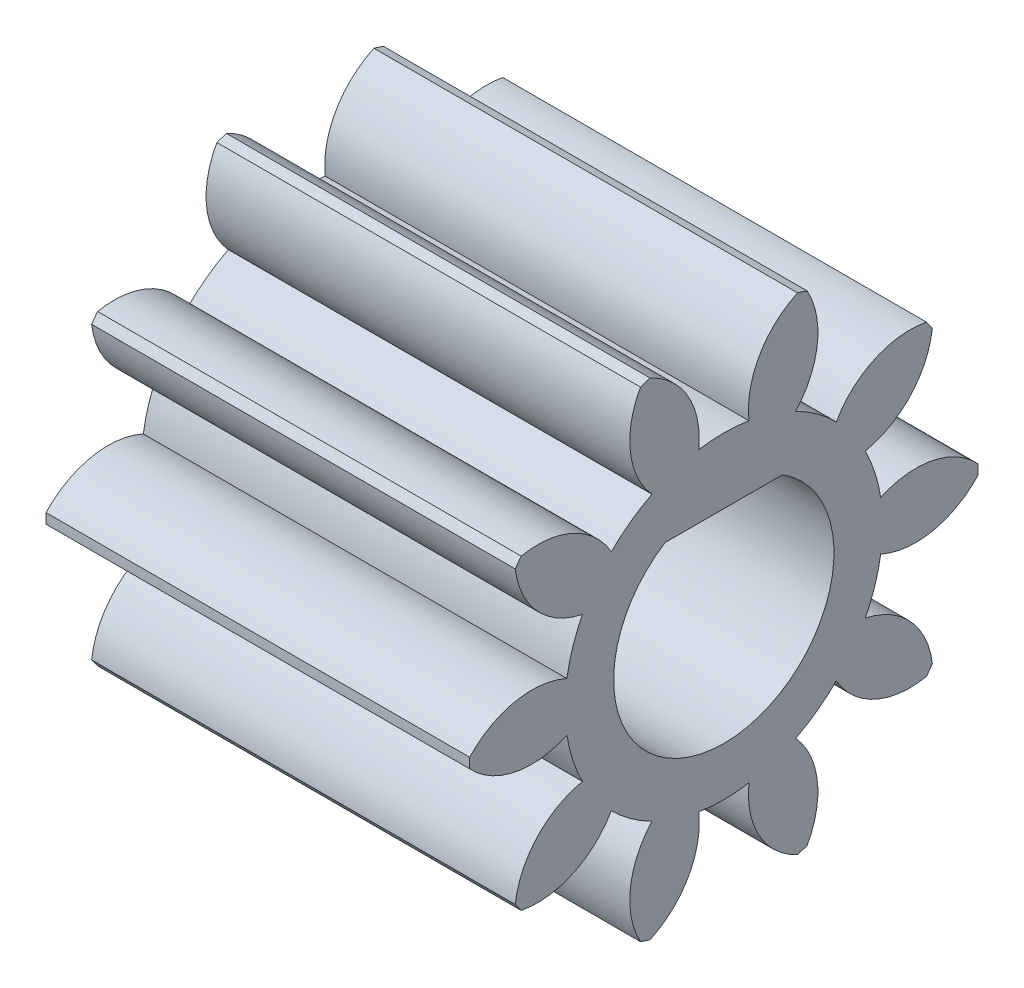
SolidWorks part; units mm, degrees
ref_plane "Plane1" through (0, 0, 0) normal (0, 0, 1) x (1, 0, 0)
ref_plane "Plane2" through (0, 0, 0) normal (0, 1, 0) x (1, 0, 0)
ref_plane "Plane3" through (0, 0, 0) normal (1, 0, 0) x (0, 0, -1)
other "Configuration Table"
sketch "HoldingSke" plane through (0, 0, 0) normal (0, 1, 0) x (1, 0, 0)
  line L0 (0, 0) -> (0.9848, -0.1736)
  line L1 (-15, 0) -> (100, 0) construction
  line L2 (0, 0) -> (-2.1039, 2.3779)
  line L3 (0, 0) -> (-11.863, 4.5341)
  line L4 (0, 0) -> (8.5048, 1.4996)
  line L5 (0, 0) -> (-46.8476, -17.4728)
  line L6 (0, 0) -> (-8.2896, -5.593)
  line L7 (-2.1039, 2.3779) -> (8.6586, 51.2059)
  line L8 (-76.2, 54.61) -> (-75.3, 54.61)
  line L9 (-71.009, 38.7566) -> (-53.1078, 45.2721)
  line L10 (-76.2, 71.12) -> (104.1128, 71.12)
  line L11 (0, 0) -> (-10, 0)
  line L12 (-76.2, 101.6) -> (-76.162, 101.6)
  line L13 (24.9733, 27.94) -> (52.9518, 28.4284)
  line L14 (24.9733, 27.94) -> (24.9743, 27.94)
  line L15 (24.9733, 27.94) -> (100.4006, 29.5858)
  line L16 (-63.627, -1) -> (-12.827, -1)
  circle A0 centre (0, 0) radius 2.5
  circle A1 centre (0, 0) radius 3.749
  circle A2 centre (0, 0) radius 37.5
  circle A3 centre (0, 0) radius 2.5
  dimension "MHD" = 7.498
  dimension "Hub_dia" = 75
  dimension "Bore" = 5
  dimension "MBD" = 5
  dimension "Num_teeth" = 10
  dimension "Pitch" = 1
  dimension "Overall_len" = 50
  dimension "Show_teeth" = 10
  dimension "Thickness" = 10
  dimension "OAL" = 50.0001
  dimension "T_dim" = 0.9
  dimension "Ap" = 20
  dimension "H" = 19.05
  dimension "Pitch_radius" = 180.3128
  dimension "Width" = 10
  dimension "Backlash" = 0.038
  dimension "Addendum_fac" = 1
  dimension "Dedendum_fac" = 1.25
  dimension "Clearance_fac" = 0.25
  dimension "Dedendum_add" = 0.001
  dimension "Module" = 1
sketch "BasProSke" plane through (0, 0, 0) normal (0, 1, 0) x (1, 0, 0)
  line L0 (-10, 0) -> (60, 0) construction
  line L1 (0, 0) -> (0, 6)
  line L2 (0, 0) -> (10, 0)
  line L3 (10, 0) -> (10, 6)
  line L4 (10, 6) -> (0, 6)
  dimension "Thickness" = 10
  dimension "Diameter" = 12
revolve "Base-Revolve" add sketch "BasProSke" angle 360 about L0
sketch "TooCutSke" plane through (0, 0, 0) normal (1, 0, 0) x (0, 0, -1)
  line L1 (0, 0) -> (0, 107) construction
  line L2 (0, 0) -> (-0.8485, 4.9275) construction
  line L3 (0, 0) -> (-3.0584, 9.4126) construction
  line L4 (-0.8485, 4.9275) -> (-1.5292, 4.7063) construction
  arc A0 (0.5928, 3.7018) -> (-0.5928, 3.7018) centre (0, 0) ccw
  arc A1 (1.7758, 5.7578) -> (-1.7758, 5.7578) centre (0, 0) ccw
  circle A2 centre (0, 0) radius 5 construction
  circle A3 centre (0, 0) radius 4.6985 construction
  arc A4 (-0.5928, 3.7018) -> (-1.7758, 5.7578) centre (-2.5801, 3.9267) ccw
  arc A5 (1.7758, 5.7578) -> (0.5928, 3.7018) centre (2.5801, 3.9267) ccw
  dimension "Root_dia" = 7.498
  dimension "Overcut_dia" = 12.0508
  dimension "Pitch_dia" = 10
  dimension "Base_dia" = 9.3969
  dimension "Flank_rad" = 2
  dimension "Half_ang" = 18
  dimension "Half_CT" = 0.7157
extrude "ToothCut" cut sketch "TooCutSke" along normal through all
fillet "Breaks" [suppressed] radius 0.02
fillet "RootFillets" [suppressed] radius 0.251
pattern_circular "TeethCuts" count 10 every 36 about axis through (-10, 0, 0) along (1, 0, 0) of "ToothCut", "RootFillets", "Breaks"
sketch "HubNeaOneSke" plane through (0, 0, 0) normal (-1, 0, 0) x (0, 0, 1)
  circle A0 centre (0, 0) radius 3.749
  dimension "Diameter" = 7.498
extrude "HubNearOne" [suppressed] add sketch "HubNeaOneSke" along normal blind 40.0001
sketch "HubNeaBotSke" plane through (0, 0, 0) normal (-1, 0, 0) x (0, 0, 1)
  circle A0 centre (0, 0) radius 3.749
  dimension "Diameter" = 7.498
extrude "HubNearBoth" [suppressed] add sketch "HubNeaBotSke" along normal blind 20
ref_plane "FarPln" through (10, 0, 0) normal (1, 0, 0) x (0, 0, -1)
sketch "HubFarSke" plane through (10, 0, 0) normal (1, 0, 0) x (0, 0, -1)
  circle A0 centre (0, 0) radius 3.749
  dimension "Diameter" = 7.498
extrude "HubFar" [suppressed] add sketch "HubFarSke" along normal blind 20
sketch "BorSke" plane through (0, 0, 0) normal (1, 0, 0) x (0, 0, -1)
  circle A0 centre (0, 0) radius 2.5
  dimension "Diameter" = 5
extrude "Bore" cut sketch "BorSke" along normal mid plane 100.0001
sketch "KeySke" plane through (0, 0, 0) normal (1, 0, 0) x (0, 0, -1)
  line L0 (-1, 0) -> (-1, 3.4)
  line L1 (-1, 3.4) -> (1, 3.4)
  line L2 (1, 3.4) -> (1, 0)
  line L3 (0, 0) -> (0, 34) construction
  line L4 (-1, 0) -> (1, 0)
  dimension "Offset" = 3.4
  dimension "Width" = 2
extrude "Keyway" [suppressed] cut sketch "KeySke" along normal mid plane 100.0001
pattern_circular "Keyway2" [suppressed] count 2 every 90 about axis through (-10, 0, 0) along (1, 0, 0)
sketch "Sketch1" plane through (10, 0, 0) normal (1, 0, 0) x (0, 0, -1)
  line L0 (0, 0) -> (2.4, 0) construction
  line L1 (2.4, 0.7) -> (2.4, -0.7) construction
  circle A0 centre (0, 0) radius 2.5
  point P7 (2.4, 0)
extrude "Boss-Extrude1" add sketch "Sketch1" against normal blind 10
sketch "Sketch2" plane through (0, 0, 0) normal (-1, 0, 0) x (0, 0, 1)
  line L0 (0, 0) -> (0, 2.2) construction
  line L1 (-1.1874, 2.2) -> (1.1874, 2.2)
  circle A0 centre (0, 0) radius 2.5
  point P7 (0, 2.2)
extrude "Cut-Extrude2" cut sketch "Sketch2" against normal blind 10
sketch "Sketch3" plane through (0, 0, 0) normal (-1, 0, 0) x (0, 0, 1)
  line L0 (-1.3856, 2.2) -> (1.3856, 2.2)
  arc A0 (-1.1874, 2.2) -> (1.1874, 2.2) centre (0, 0) ccw construction
  arc A1 (-1.1874, 2.2) -> (1.1874, 2.2) centre (0, 0) ccw
  arc A2 (-1.3856, 2.2) -> (1.3856, 2.2) centre (0, 0) ccw
  arc A3 (-1.2349, 2.288) -> (1.2349, 2.288) centre (0, 0) ccw construction
  point P9 (0, 2.2)
  dimension "D1" = 0.1
extrude "Cut-Extrude4" cut sketch "Sketch3" against normal blind 12.8 contours A2 L0
equation "' \"Module@HoldingSke\" = 6.35"
equation "' \"Num_teeth@HoldingSke\" = 12"
equation "' \"Ap@HoldingSke\" =  20"
equation "' \"Ap@HoldingSke\" = 20"
equation "' \"Width@HoldingSke\" = 0.5 * 25.4"
equation "' \"Hub_dia@HoldingSke\"= 1 * 25.4"
equation "' \"Hub_dia@HoldingSke\" = 1 * 25.4"
equation "' \"Overall_len@HoldingSke\" = 1.0 * 25.4"
equation "' \"Bore@HoldingSke\" = 0.75 * 25.4"
equation "' \"T_dim@HoldingSke\" = 0.1 * 25.4"
equation "' \"Width@KeySke\" = 0.25 * 25.4"
equation "' \"Show_teeth@HoldingSke\" = 13"
equation "' \"Backlash@HoldingSke\" = 0.009 * 25.4"
equation "' \"Addendum_fac@HoldingSke\" = 1.0"
equation "' \"Dedendum_fac@HoldingSke\" = 1.25"
equation "' \"Dedendum_add@HoldingSke\" = 0.00005 * 25.4"
equation "' \"Clearance_fac@HoldingSke\" = 0.25"
equation "\"Pitch@HoldingSke\" = 1 / \"Module@HoldingSke\""
equation "\"Overcut_dia@TooCutSke\" = (\"Num_teeth@HoldingSke\" + 2 * \"Addendum_fac@HoldingSke\") / \"Pitch@HoldingSke\" + 0.002 * 25.4"
equation "\"Pitch_dia@TooCutSke\" = \"Num_teeth@HoldingSke\" / \"Pitch@HoldingSke\""
equation "\"Base_dia@TooCutSke\" = \"Num_teeth@HoldingSke\" / \"Pitch@HoldingSke\" * cos((\"Ap@HoldingSke\"  * 3.14159265 / 180))"
equation "\"Root_dia@TooCutSke\" = (\"Num_teeth@HoldingSke\" + 2) / \"Pitch@HoldingSke\" - 2 * (\"Addendum_fac@HoldingSke\" + \"Dedendum_fac@HoldingSke\") / \"Pitch@HoldingSke\" - \"Dedendum_add@HoldingSke\" * 2"
equation "\"Half_ang@TooCutSke\" = 180 / \"Num_teeth@HoldingSke\""
equation "\"Half_CT@TooCutSke\" = \"Num_teeth@HoldingSke\" / \"Pitch@HoldingSke\" * sin((3.14159265 / 2 / \"Num_teeth@HoldingSke\")) / 2 - 7 * \"Backlash@HoldingSke\" / 4"
equation "\"Flank_rad@TooCutSke\" = \"Num_teeth@HoldingSke\" / \"Pitch@HoldingSke\" / 5"
equation "\"Radius@RootFillets\" = \"Clearance_fac@HoldingSke\" / \"Pitch@HoldingSke\" + \"Dedendum_add@HoldingSke\""
equation "\"Break_rad@Breaks\" = 0.02 / \"Pitch@HoldingSke\""
equation "\"Thickness@HoldingSke\" = \"Width@HoldingSke\""
equation "\"OAL@HoldingSke\" = \"Thickness@HoldingSke\""
equation "\"MHD@HoldingSke\" = (\"Num_teeth@HoldingSke\" + 2) / \"Pitch@HoldingSke\" - 2 * (\"Addendum_fac@HoldingSke\" + \"Dedendum_fac@HoldingSke\")  / \"Pitch@HoldingSke\" - \"Dedendum_add@HoldingSke\" * 2"
equation "\"MBD@HoldingSke\" = (\"Num_teeth@HoldingSke\" + 2) / \"Pitch@HoldingSke\" - 2 * (\"Addendum_fac@HoldingSke\" + \"Dedendum_fac@HoldingSke\")  / \"Pitch@HoldingSke\" - \"Dedendum_add@HoldingSke\" * 2 - 0.002 * 25.4"
equation "\"MHD@HoldingSke\" = ((sgn( \"MHD@HoldingSke\" - \"Hub_dia@HoldingSke\" )-1)*( \"MHD@HoldingSke\" - \"Hub_dia@HoldingSke\" ))/-2+ \"Hub_dia@HoldingSke\""
equation "\"MBD@HoldingSke\" = ((sgn( \"MBD@HoldingSke\" - \"Bore@HoldingSke\" )-1)*( \"MBD@HoldingSke\" - \"Bore@HoldingSke\" ))/-2+ \"Bore@HoldingSke\""
equation "\"OAL@HoldingSke\" = ((sgn( \"OAL@HoldingSke\" - \"Overall_len@HoldingSke\" )+1)*( \"OAL@HoldingSke\" - \"Overall_len@HoldingSke\" ))/2 + \"Overall_len@HoldingSke\" + 0.000002 * 25.4"
equation "\"Num_teeth@TeethCuts\" = int( \"Show_teeth@HoldingSke\" ) + 1"
equation "\"Num_teeth@TeethCuts\" = ((sgn( \"Num_teeth@TeethCuts\" - \"Num_teeth@HoldingSke\" )-1)*( \"Num_teeth@TeethCuts\" - \"Num_teeth@HoldingSke\" ))/-2+ \"Num_teeth@HoldingSke\""
equation "\"Num_teeth@TeethCuts\" = ((sgn( \"Num_teeth@TeethCuts\" - 2.0)+1)*( \"Num_teeth@TeethCuts\" - 2.0))/2 +2.0"
equation "\"Angle@TeethCuts\" = 360.0 / \"Num_teeth@HoldingSke\""
equation "\"Diameter@BasProSke\" = (\"Num_teeth@HoldingSke\" + 2 * \"Addendum_fac@HoldingSke\") / \"Pitch@HoldingSke\""
equation "\"Thickness@BasProSke\"  = \"Thickness@HoldingSke\""
equation "' \"Fillet_rad@BasProSke\" =  \"Thickness@HoldingSke\" * 0.05"
equation "' \"Fillet_rad@BasProSke\" = \"Thickness@HoldingSke\" * 0.05"
equation "\"MHD@HoldingSke\" = ((sgn( \"MHD@HoldingSke\" - \"Root_dia@TooCutSke\" )-1)*( \"MHD@HoldingSke\" - \"Root_dia@TooCutSke\" ))/-2+ \"Root_dia@TooCutSke\""
equation "\"Diameter@HubNeaOneSke\" = \"MHD@HoldingSke\""
equation "\"Length@HubNearOne\" = \"OAL@HoldingSke\" - \"Thickness@BasProSke\""
equation "\"Diameter@HubNeaBotSke\" = \"MHD@HoldingSke\""
equation "\"Length@HubNearBoth\" = ( \"OAL@HoldingSke\" - \"Thickness@BasProSke\" ) / 2.0"
equation "\"Thickness@FarPln\" = \"Thickness@BasProSke\""
equation "\"Diameter@HubFarSke\" = \"MHD@HoldingSke\""
equation "\"Length@HubFar\" = ( \"OAL@HoldingSke\" - \"Thickness@BasProSke\" ) / 2.0"
equation "\"Diameter@BorSke\" = \"MBD@HoldingSke\""
equation "\"D1@Bore\" = \"OAL@HoldingSke\" * 2.0"
equation "\"D1@Keyway\" = \"OAL@HoldingSke\" * 2.0"
equation "\"Offset@KeySke\" = \"T_dim@HoldingSke\" + \"MBD@HoldingSke\" / 2.0"
